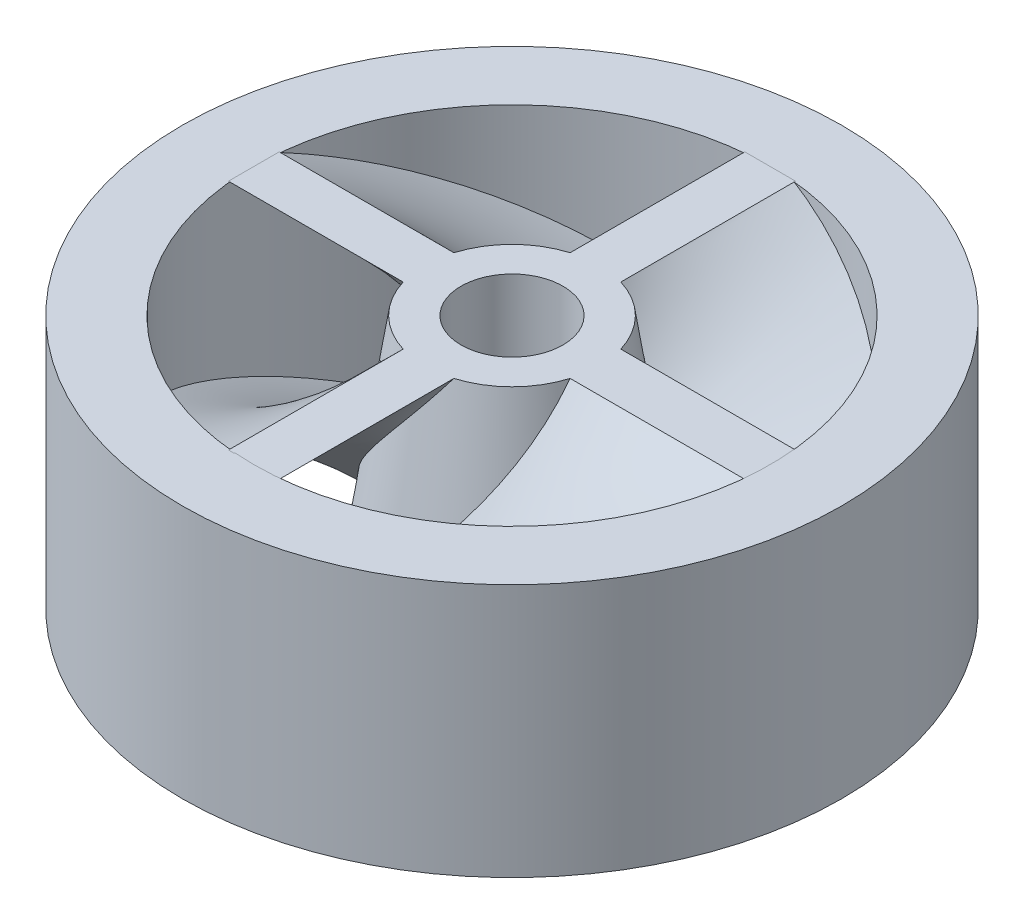
SolidWorks part; units mm, degrees
material "6061-T6 (SS)"
ref_plane "Front Plane" through (0, 0, 0) normal (0, 0, 1) x (1, 0, 0)
ref_plane "Top Plane" through (0, 0, 0) normal (0, 1, 0) x (1, 0, 0)
ref_plane "Right Plane" through (0, 0, 0) normal (1, 0, 0) x (0, 0, -1)
ref_axis "Axis1" through (0, 28.9225, 0) along (0, -1, 0)
sketch "Sketch1" plane through (0, 0, 0) normal (0, 1, 0) x (1, 0, 0)
  circle A0 centre (0, 0) radius 12.9286
  dimension "D1" = 25.8572
curve "Helix/Spiral1" pitch 38.862 height 12.7 turns 0.3268
sketch "Sketch2" plane through (0, 0, 0) normal (0, 1, 0) x (1, 0, 0)
  line L0 (-1.27, -12.9286) -> (1.27, -12.9286)
  line L1 (1.27, 0) -> (-1.27, 0)
  line L2 (1.27, 0) -> (1.27, -12.9286)
  line L4 (-1.27, 0) -> (-1.27, -12.9286)
  point P4 (0, -12.9286)
  dimension "D2" = 2.54
  dimension "D1" = 12.9286
sweep "Sweep1" add profiles "Sketch2" path "Helix/Spiral1"
sketch "Sketch4" plane through (0, 0, 0) normal (0, 0, 1) x (1, 0, 0)
  line L0 (0, 0) -> (0, -12.7002)
  line L1 (0, 0) -> (4.3688, 0)
  line L2 (4.3688, 0) -> (6.35, -12.7002)
  line L3 (0, -12.7002) -> (-4.9832, -12.7002) construction
  line L4 (0, -12.7002) -> (6.35, -12.7002)
  spline S0 degree 1 poles (0.5892, -12.7) (-0.5892, -12.7004) knots 0 0 1 1 construction
  dimension "D1" = 4.3688
  dimension "D2" = 6.35
revolve "Revolve1" add sketch "Sketch4" angle 360 about L0
pattern_circular "CirPattern1" count 4 over 360 about axis through (0, 28.9225, 0) along (0, -1, 0) of "Sweep1"
hole_wizard "#10 Clearance Hole1" positions "3DSketch2" profile "Sketch9" hole size "#10" standard "ANSI Inch" end condition through all
sketch3d "3DSketch2"
  point P0 (0, 0, 0)
sketch "Sketch9" plane through (0, 0, 0) normal (1, 0, 0) x (0, 0, 1)
  line L0 (0, 0) -> (0, 12.7574)
  line L1 (0, 12.7574) -> (2.5527, 12.7574)
  line L2 (2.5527, 12.7574) -> (2.5527, 0)
  line L5 (2.5527, 0) -> (0, 0)
  line L11 (0, -6.35) -> (0, 107.95) construction
  dimension "Thru Hole Dia." = 5.1054
  dimension "Thru Hole Depth" = 12.7574
sketch "Sketch11" plane through (0, 0, 0) normal (0, 0, 1) x (1, 0, 0)
  line L1 (12.9286, 0) -> (16.51, 0)
  line L2 (12.9286, 0) -> (12.9286, -12.7)
  line L3 (12.9286, -12.7) -> (16.51, -12.7)
  line L4 (16.51, 0) -> (16.51, -12.7)
  line L6 (16.51, 0) -> (16.51, 6.1214)
  dimension "D1" = 12.7
  dimension "D2" = 12.9286
  dimension "D3" = 16.51
revolve "Revolve2" add sketch "Sketch11" angle 360 about axis through (0, 28.9225, 0) along (0, -1, 0)
equation "\"Height\"= 1 / 2"
equation "\"Tip Radius\"= .509"
equation "\"Hub Base Radius\"= .25"
equation "\"Blade Lead\"= 1.53"
equation "\"Axial Clearance\"= .381"
equation "\"D1@Sketch1\"= 2 * \"Tip Radius\""
equation "\"D1@Sketch2\"=\"Tip Radius\""
equation "\"D1@Sketch11\"=\"Height\""
equation "\"D2@Sketch11\"=\"Tip Radius\""
equation "\"Hub Top Radius\"=0.172"
equation "\"D1@Sketch4\"=\"Hub Top Radius\""
equation "\"D3@Sketch11\"= \"Inducer OD@[TP] [Pump] [Ox] Pump.Assembly\" / 2"
